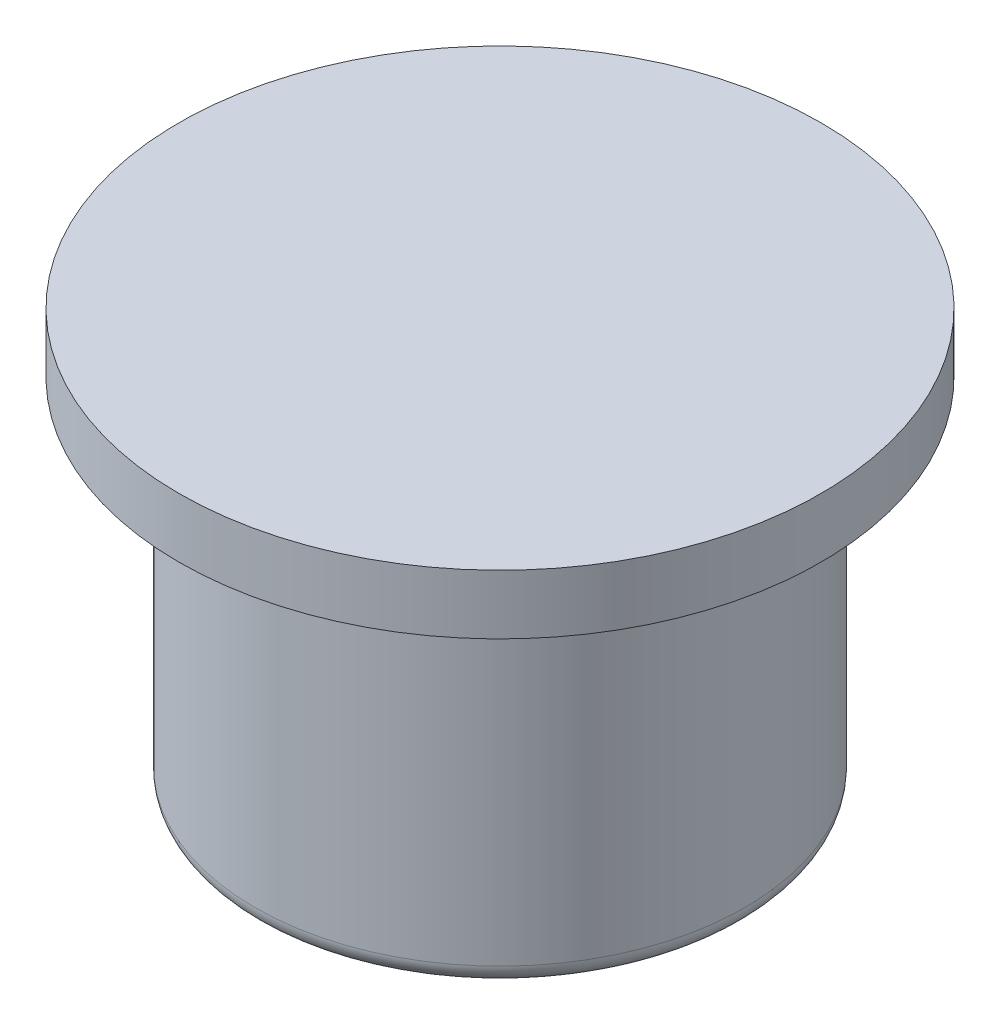
SolidWorks part; units mm, degrees
ref_plane "Front Plane" through (0, 0, 0) normal (0, 0, 1) x (1, 0, 0)
ref_plane "Top Plane" through (0, 0, 0) normal (0, 1, 0) x (1, 0, 0)
ref_plane "Right Plane" through (0, 0, 0) normal (1, 0, 0) x (0, 0, -1)
sketch "Sketch1" plane through (0, 0, 0) normal (0, 1, 0) x (1, 0, 0)
  circle A0 centre (0, 0) radius 3.1374
extrude "Boss-Extrude1" add sketch "Sketch1" along normal blind 4.572
fillet "Fillet3" radius 0.254 1 edges at (0, 0, 3.1374)
sketch "Sketch2" plane through (0, 4.572, 0) normal (0, 1, 0) x (1, 0, 0)
  circle A0 centre (0, 0) radius 4.1115
extrude "Boss-Extrude3" add sketch "Sketch2" along normal blind 0.762
